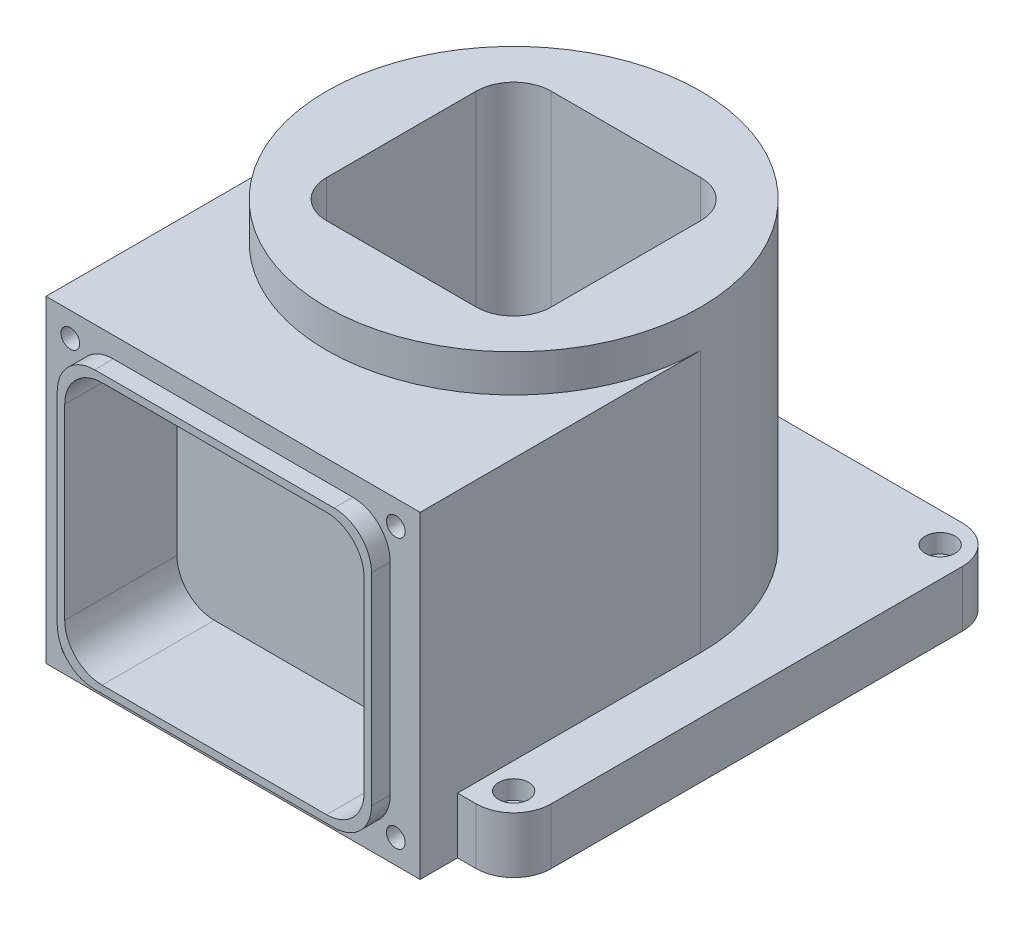
SolidWorks part; units mm, degrees
ref_plane "Front Plane" through (0, 0, 0) normal (0, 0, 1) x (1, 0, 0)
ref_plane "Top Plane" through (0, 0, 0) normal (0, 1, 0) x (1, 0, 0)
ref_plane "Right Plane" through (0, 0, 0) normal (1, 0, 0) x (0, 0, -1)
sketch "Sketch1" plane through (0, 0, 0) normal (0, 1, 0) x (1, 0, 0)
  line L1 (-65, 65) -> (65, 65)
  line L2 (-65, 65) -> (-65, -65)
  line L3 (-65, -65) -> (65, -65)
  line L4 (65, 65) -> (65, -65)
  line L5 (-65, 65) -> (65, -65) construction
  line L6 (-65, -65) -> (65, 65) construction
  point P0 (0, 0)
  dimension "D1" = 130
extrude "Boss-Extrude1" add sketch "Sketch1" along normal blind 15
sketch "Sketch2" plane through (0, 15, 0) normal (0, 1, 0) x (1, 0, 0)
  circle A0 centre (0, 0) radius 50
  dimension "D1" = 100
extrude "Boss-Extrude2" add sketch "Sketch2" along normal blind 80
sketch "Sketch3" plane through (0, 0, 0) normal (1, 0, 0) x (0, 0, -1)
  line L1 (0, 0) -> (-75, 0)
  line L2 (0, 0) -> (0, 85)
  line L3 (0, 85) -> (-75, 85)
  line L4 (-75, 0) -> (-75, 85)
  dimension "D1" = 75
  dimension "D2" = 85
extrude "Boss-Extrude3" add sketch "Sketch3" along normal mid plane 100
sketch "Sketch4" plane through (0, 95, 0) normal (0, 1, 0) x (1, 0, 0)
  line L1 (-20, 30) -> (20, 30)
  line L2 (-30, 20) -> (-30, -20)
  line L3 (-20, -30) -> (20, -30)
  line L4 (30, 20) -> (30, -20)
  line L5 (-30, 30) -> (30, -30) construction
  line L6 (-30, -30) -> (30, 30) construction
  arc A0 (-30, -20) -> (-20, -30) centre (-20, -20) ccw
  arc A1 (20, -30) -> (30, -20) centre (20, -20) ccw
  arc A2 (20, 30) -> (30, 20) centre (20, 20) cw
  arc A3 (-20, 30) -> (-30, 20) centre (-20, 20) ccw
  point P0 (0, 0)
  dimension "D2" = 10
  dimension "D1" = 60
extrude "Cut-Extrude2" cut sketch "Sketch4" against normal blind 60
sketch "Sketch5" plane through (0, 0, 75) normal (0, 0, 1) x (1, 0, 0)
  line L0 (0, 85) -> (0, 0) construction
  line L1 (50, 85) -> (-50, 85) construction
  line L3 (-30, 77.5) -> (30, 77.5)
  line L4 (-40, 67.5) -> (-40, 17.5)
  line L5 (-30, 7.5) -> (30, 7.5)
  line L6 (40, 67.5) -> (40, 17.5)
  line L7 (-40, 77.5) -> (40, 7.5) construction
  line L8 (-40, 7.5) -> (40, 77.5) construction
  arc A0 (-40, 17.5) -> (-30, 7.5) centre (-30, 17.5) ccw
  arc A1 (30, 7.5) -> (40, 17.5) centre (30, 17.5) ccw
  arc A2 (30, 77.5) -> (40, 67.5) centre (30, 67.5) cw
  arc A3 (-30, 77.5) -> (-40, 67.5) centre (-30, 67.5) ccw
  point P5 (0, 42.5)
  dimension "D3" = 10
  dimension "D1" = 80
  dimension "D2" = 70
extrude "Cut-Extrude4" cut sketch "Sketch5" against normal blind 25
sketch "Sketch6" plane through (0, 0, 75) normal (0, 0, 1) x (1, 0, 0)
  line L0 (-50, 85) -> (-50, 0) construction
  line L1 (50, 85) -> (-50, 85) construction
  line L2 (50, 85) -> (50, 0) construction
  line L3 (-40, 42.5) -> (40, 42.5) construction
  line L4 (-40, 67.5) -> (-40, 17.5) construction
  line L5 (40, 17.5) -> (40, 67.5) construction
  circle A0 centre (-43.5, 78.5) radius 2.5
  circle A1 centre (43.5, 78.5) radius 2.5
  circle A2 centre (43.5, 6.5) radius 2.5
  circle A3 centre (-43.5, 6.5) radius 2.5
  dimension "D1" = 5
  dimension "D2" = 6.5
  dimension "D3" = 6.5
  dimension "D4" = 6.5
extrude "Cut-Extrude5" cut sketch "Sketch6" against normal blind 35
fillet "Fillet1" radius 10 4 edges at (-65, 7.5, -65) (-65, 7.5, 65) (65, 7.5, -65) (65, 7.5, 65)
sketch "Sketch7" plane through (0, 0, 75) normal (0, 0, 1) x (1, 0, 0)
  line L0 (0, 77.5) -> (0, 7.5) construction
  line L1 (30, 77.5) -> (-30, 77.5) construction
  line L2 (-30, 7.5) -> (30, 7.5) construction
  line L4 (-32, 79.5) -> (32, 79.5)
  line L5 (-42, 69.5) -> (-42, 15.5)
  line L6 (-32, 5.5) -> (32, 5.5)
  line L7 (42, 69.5) -> (42, 15.5)
  line L8 (-42, 79.5) -> (42, 5.5) construction
  line L9 (-42, 5.5) -> (42, 79.5) construction
  line L10 (-30, 77.5) -> (30, 77.5)
  line L11 (-40, 67.5) -> (-40, 17.5)
  line L12 (-30, 7.5) -> (30, 7.5)
  line L13 (40, 67.5) -> (40, 17.5)
  line L14 (-40, 77.5) -> (40, 7.5) construction
  line L15 (-40, 7.5) -> (40, 77.5) construction
  arc A0 (-42, 15.5) -> (-32, 5.5) centre (-32, 15.5) ccw
  arc A1 (32, 5.5) -> (42, 15.5) centre (32, 15.5) ccw
  arc A2 (32, 79.5) -> (42, 69.5) centre (32, 69.5) cw
  arc A3 (-32, 79.5) -> (-42, 69.5) centre (-32, 69.5) ccw
  arc A4 (30, 7.5) -> (40, 17.5) centre (30, 17.5) ccw
  arc A5 (30, 77.5) -> (40, 67.5) centre (30, 67.5) cw
  arc A6 (-30, 77.5) -> (-40, 67.5) centre (-30, 67.5) ccw
  arc A7 (-40, 17.5) -> (-30, 7.5) centre (-30, 17.5) ccw
  point P6 (0, 42.5)
  point P23 (0, 42.5)
  dimension "D3" = 10
  dimension "D6" = 10
  dimension "D7" = 10
  dimension "D1" = 74
  dimension "D2" = 84
  dimension "D4" = 70
  dimension "D5" = 80
extrude "Boss-Extrude5" add sketch "Sketch7" along normal blind 5
sketch "Sketch8" plane through (0, 15, 0) normal (0, 1, 0) x (1, 0, 0)
  line L0 (-65, 55) -> (-65, -55) construction
  line L1 (55, 65) -> (-55, 65) construction
  line L2 (-55, -65) -> (-50, -65) construction
  line L3 (0, 30) -> (0, -30) construction
  line L4 (20, 30) -> (-20, 30) construction
  line L5 (-20, -30) -> (20, -30) construction
  circle A0 centre (-57, 57) radius 2.5
  circle A1 centre (-57, -57) radius 2.5
  circle A4 centre (57, -57) radius 2.5
  circle A5 centre (57, 57) radius 2.5
  dimension "D1" = 5
  dimension "D2" = 8
  dimension "D3" = 8
  dimension "D4" = 8
  dimension "D5" = 8
extrude "Cut-Extrude6" cut sketch "Sketch8" against normal through all
sketch "Sketch9" plane through (0, 15, 0) normal (0, 1, 0) x (1, 0, 0)
  circle A0 centre (-57, 57) radius 4
  circle A1 centre (57, 57) radius 4
  circle A2 centre (-57, -57) radius 4
  circle A3 centre (57, -57) radius 4
  dimension "D1" = 8
extrude "Cut-Extrude7" cut sketch "Sketch9" against normal blind 5
